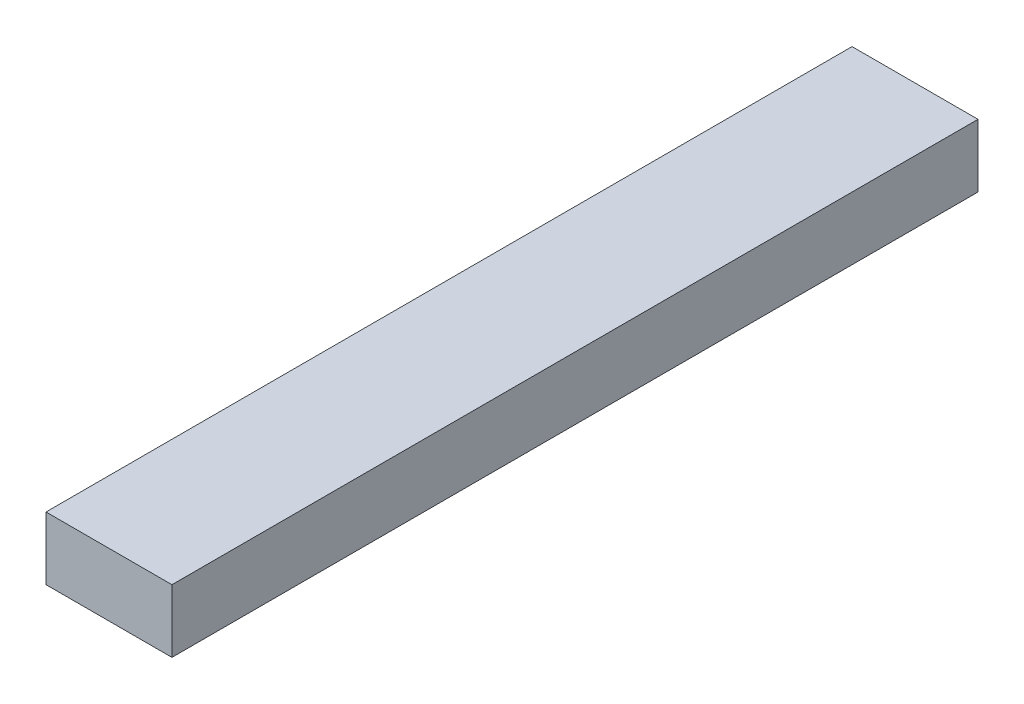
SolidWorks part; units mm, degrees
ref_plane "Front Plane" through (0, 0, 0) normal (0, 0, 1) x (1, 0, 0)
ref_plane "Top Plane" through (0, 0, 0) normal (0, 1, 0) x (1, 0, 0)
ref_plane "Right Plane" through (0, 0, 0) normal (1, 0, 0) x (0, 0, -1)
sketch "Sketch1" plane through (0, 0, 0) normal (0, 0, 1) x (1, 0, 0)
  line L1 (-50, -25) -> (50, -25)
  line L2 (-50, -25) -> (-50, 25)
  line L3 (-50, 25) -> (50, 25)
  line L4 (50, -25) -> (50, 25)
  line L5 (-50, -25) -> (50, 25) construction
  line L6 (-50, 25) -> (50, -25) construction
  point P0 (0, 0)
  dimension "D1" = 100
  dimension "D2" = 50
extrude "Boss-Extrude1" add sketch "Sketch1" along normal blind 640
